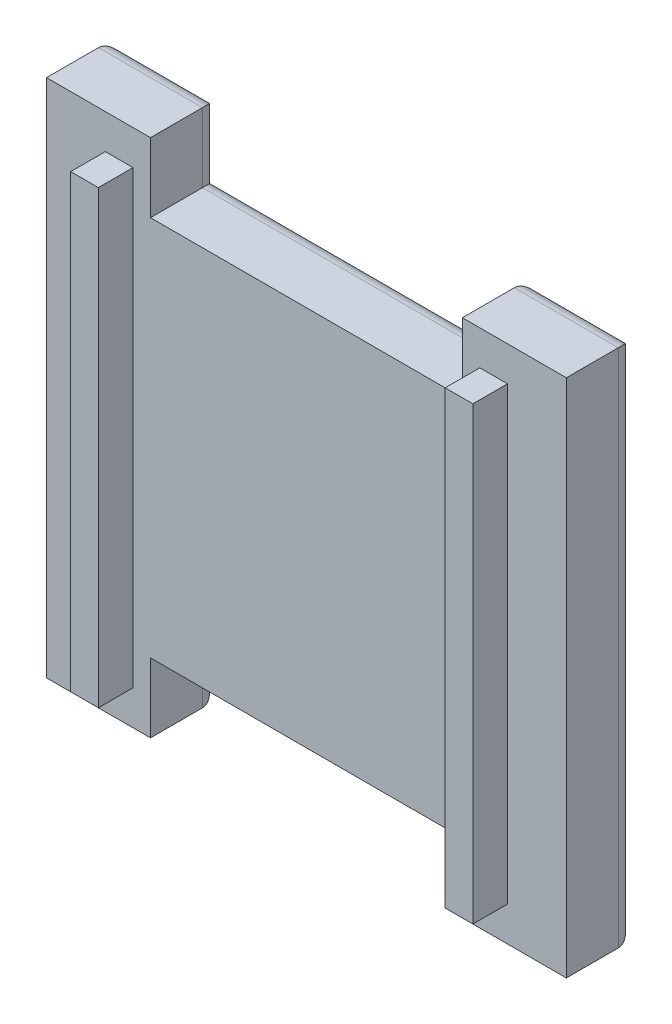
SolidWorks part; units mm, degrees
ref_plane "Front Plane" through (0, 0, 0) normal (0, 0, 1) x (1, 0, 0)
ref_plane "Top Plane" through (0, 0, 0) normal (0, 1, 0) x (1, 0, 0)
ref_plane "Right Plane" through (0, 0, 0) normal (1, 0, 0) x (0, 0, -1)
sketch "Sketch1" plane through (0, 0, 0) normal (0, 0, 1) x (1, 0, 0)
  line L1 (-18.0873, 12.7486) -> (20.0127, 12.7486)
  line L2 (-18.0873, 12.7486) -> (-18.0873, -25.3514)
  line L3 (-18.0873, -25.3514) -> (20.0127, -25.3514)
  line L4 (20.0127, 12.7486) -> (20.0127, -25.3514)
  dimension "D1" = 38.1
  dimension "D2" = 38.1
extrude "Boss-Extrude1" add sketch "Sketch1" along normal blind 5.08
sketch "Sketch5" plane through (0, 0, 5.08) normal (0, 0, 1) x (1, 0, 0)
  line L0 (-18.0873, -25.3514) -> (20.0127, -25.3514) construction
  line L1 (15.7027, -22.8114) -> (13.6707, -22.8114)
  line L2 (15.7027, -22.8114) -> (15.7027, 10.2086)
  line L3 (15.7027, 10.2086) -> (13.6707, 10.2086)
  line L4 (13.6707, -22.8114) -> (13.6707, 10.2086)
  line L5 (20.0127, -25.3514) -> (20.0127, 12.7486) construction
  line L6 (-18.0873, 12.7486) -> (-18.0873, -25.3514) construction
  line L7 (-11.7453, -22.8114) -> (-13.7773, -22.8114)
  line L8 (-11.7453, -22.8114) -> (-11.7453, 10.2086)
  line L9 (-11.7453, 10.2086) -> (-13.7773, 10.2086)
  line L10 (-13.7773, -22.8114) -> (-13.7773, 10.2086)
  dimension "D1" = 33.02
  dimension "D2" = 2.032
  dimension "D3" = 2.54
  dimension "D4" = 4.31
  dimension "D5" = 2.032
  dimension "D6" = 4.31
extrude "Boss-Extrude3" add sketch "Sketch5" along normal blind 2.54
sketch "Sketch6" plane through (0, 0, 0) normal (0, 0, -1) x (-1, 0, 0)
  line L0 (-20.0127, 12.7486) -> (18.0873, 12.7486) construction
  line L1 (10.4673, 12.7486) -> (-12.3927, 12.7486)
  line L2 (10.4673, 12.7486) -> (10.4673, 7.6686)
  line L3 (10.4673, 7.6686) -> (-12.3927, 7.6686)
  line L4 (-12.3927, 12.7486) -> (-12.3927, 7.6686)
  line L5 (-20.0127, -25.3514) -> (-20.0127, 12.7486) construction
  line L6 (18.0873, -25.3514) -> (-20.0127, -25.3514) construction
  line L7 (-12.3927, -25.3514) -> (10.4673, -25.3514)
  line L8 (-12.3927, -25.3514) -> (-12.3927, -20.2714)
  line L9 (-12.3927, -20.2714) -> (10.4673, -20.2714)
  line L10 (10.4673, -25.3514) -> (10.4673, -20.2714)
  dimension "D1" = 22.86
  dimension "D2" = 7.62
  dimension "D3" = 5.08
  dimension "D4" = 5.08
  dimension "D5" = 22.86
extrude "Cut-Extrude1" cut sketch "Sketch6" against normal through all
fillet "Fillet1" radius 1.27 12 edges at (-10.4673, 10.2086, 0) (0.9627, 7.6686, 0) (12.3927, 10.2086, 0) (16.2027, 12.7486, 0) (-14.2773, 12.7486, 0) (-18.0873, -6.3014, 0) (-14.2773, -25.3514, 0) (-10.4673, -22.8114, 0) (12.3927, -22.8114, 0) (0.9627, -20.2714, 0) (16.2027, -25.3514, 0) (20.0127, -6.3014, 0)
